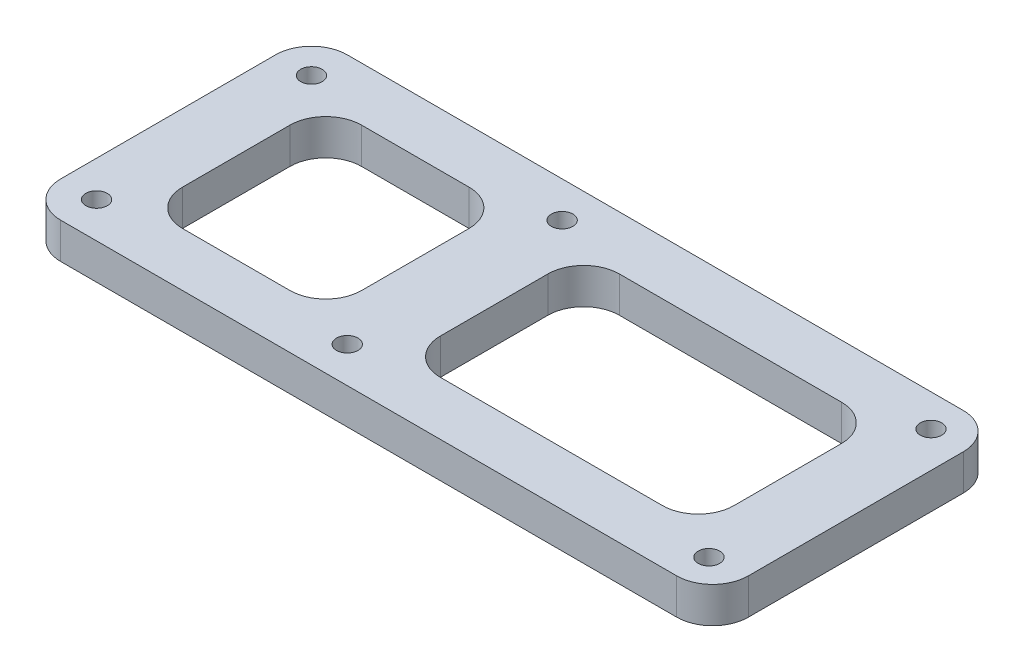
SolidWorks part; units mm, degrees
material "Acrylic (Medium-high impact)"
ref_plane "Front Plane" through (0, 0, 0) normal (0, 0, 1) x (1, 0, 0)
ref_plane "Top Plane" through (0, 0, 0) normal (0, 1, 0) x (1, 0, 0)
ref_plane "Right Plane" through (0, 0, 0) normal (1, 0, 0) x (0, 0, -1)
sketch "Sketch1" plane through (0, 0, 0) normal (0, 1, 0) x (1, 0, 0)
  line L0 (0, 15) -> (0, -15)
  line L5 (-35, 15) -> (-35, -15)
  line L6 (-40, 20) -> (56, 20)
  line L7 (-35, 15) -> (0, 15)
  line L9 (-40, 20) -> (-40, -20)
  line L11 (-40, -20) -> (56, -20)
  line L12 (56, 20) -> (56, -20)
  line L13 (-40, 0) -> (56, 0)
  line L14 (-30.5, 12.5) -> (-5.5, 12.5)
  line L15 (-30.5, 12.5) -> (-30.5, -12.5)
  line L16 (-30.5, -12.5) -> (-5.5, -12.5)
  line L17 (-5.5, 12.5) -> (-5.5, -12.5)
  line L22 (-30.5, 12.5) -> (-5.5, -12.5) construction
  line L23 (-30.5, -12.5) -> (-5.5, 12.5) construction
  line L28 (5.5, 12.5) -> (46.5, 12.5)
  line L29 (5.5, 12.5) -> (5.5, -12.5)
  line L30 (5.5, -12.5) -> (46.5, -12.5)
  line L31 (46.5, 12.5) -> (46.5, -12.5)
  line L32 (5.5, 12.5) -> (46.5, -12.5) construction
  line L33 (5.5, -12.5) -> (46.5, 12.5) construction
  circle A0 centre (-35, 15) radius 1.5
  circle A1 centre (0, 15) radius 1.5
  circle A2 centre (50.9975, -15.5) radius 1.5
  circle A5 centre (50.9975, 15.5) radius 1.5
  circle A6 centre (-35, -15) radius 1.5
  circle A7 centre (0, -15) radius 1.5
  point P0 (0, 0)
  point P21 (26, 0)
  point P23 (-18, 0)
  dimension "D10" = 3
  dimension "D11" = 3
  dimension "D12" = 3
  dimension "D20" = 3
  dimension "D21" = 3
  dimension "D22" = 3
  dimension "D23" = 15
  dimension "D2" = 30
  dimension "D3" = 56
  dimension "D4" = 30
  dimension "D5" = 15.5
  dimension "D6" = 40
  dimension "D7" = 51
  dimension "D8" = 40
  dimension "D9" = 35
  dimension "D13" = 18
  dimension "D14" = 26
  dimension "D15" = 25
  dimension "D16" = 41
  dimension "D17" = 25
  dimension "D18" = 25
  dimension "D19" = 31
extrude "Boss-Extrude1" add sketch "Sketch1" along normal blind 5
fillet "Fillet1" radius 5 12 edges at (5.5, 2.5, -12.5) (56, 2.5, -20) (56, 2.5, 20) (-40, 2.5, 20) (-40, 2.5, -20) (46.5, 2.5, 12.5) (5.5, 2.5, 12.5) (46.5, 2.5, -12.5) (-5.5, 2.5, 12.5) (-30.5, 2.5, 12.5) (-5.5, 2.5, -12.5) (-30.5, 2.5, -12.5)
